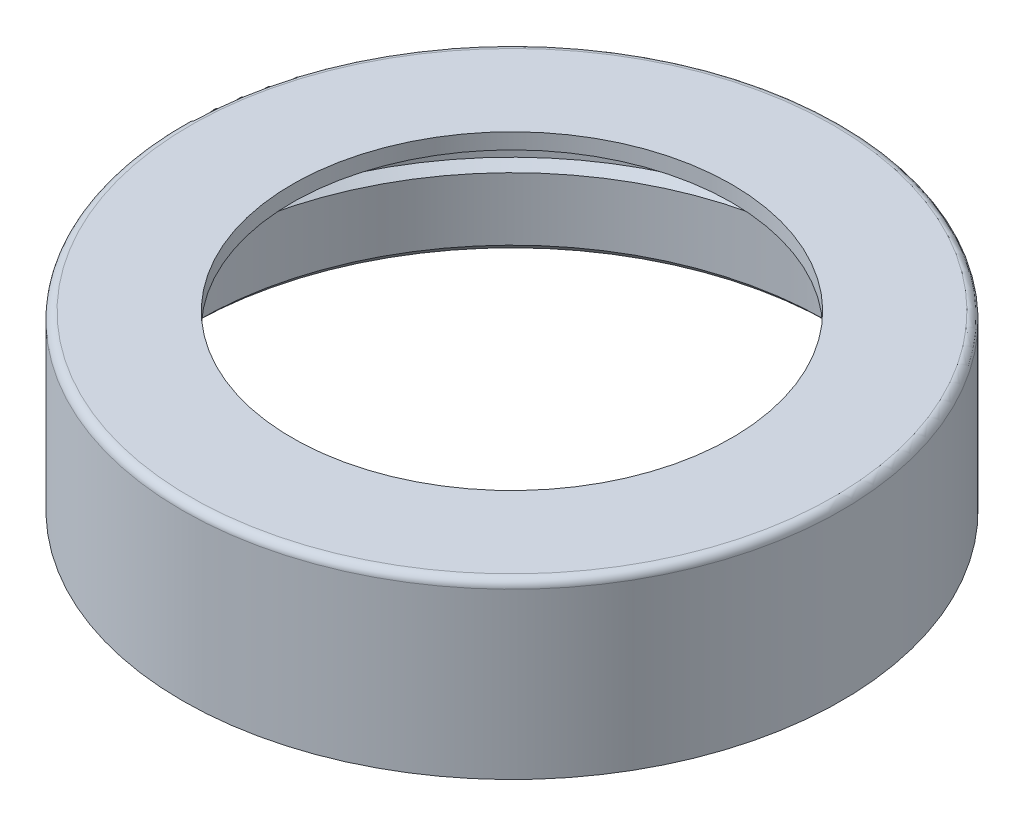
SolidWorks part; units mm, degrees
ref_plane "Plano frontal" through (0, 0, 0) normal (0, 0, 1) x (1, 0, 0)
ref_plane "Plano superior" through (0, 0, 0) normal (0, 1, 0) x (1, 0, 0)
ref_plane "Plano direito" through (0, 0, 0) normal (1, 0, 0) x (0, 0, -1)
sketch "Esboço1" plane through (0, 0, 0) normal (0, 0, 1) x (1, 0, 0)
  line L0 (-21, 0) -> (-21, 11)
  line L1 (-21, 11) -> (-14, 11)
  line L2 (-14, 11) -> (-14, 10)
  line L3 (-14, 10) -> (-20, 10)
  line L4 (-20, 10) -> (-20, 6)
  line L5 (-20.5, 0) -> (-21, 0)
  line L6 (0, 0) -> (0, 28.1917) construction
  line L7 (-20, 0.5) -> (-20.5, 0)
  line L8 (-20, 4.5) -> (-20.5, 5)
  line L9 (-20.5, 5) -> (-20.5, 6)
  line L10 (-20.5, 6) -> (-20, 6)
  line L11 (-20, 4.5) -> (-20, 0.5)
  dimension "D2" = 1
  dimension "D3" = 20
  dimension "D4" = 7
  dimension "D5" = 1
  dimension "D6" = 45
  dimension "D7" = 6
  dimension "D8" = 0.5
  dimension "D9" = 45
  dimension "D10" = 5.5
  dimension "D11" = 1
  dimension "D12" = 0.5
  dimension "D13" = 4
revolve "Revolução2" add sketch "Esboço1" angle 360 about L6
cosmetic thread "Representação de rosca1" parameters "D2"=40.1
fillet "Filete1" radius 0.5 1 edges at (0, 11, -21)
